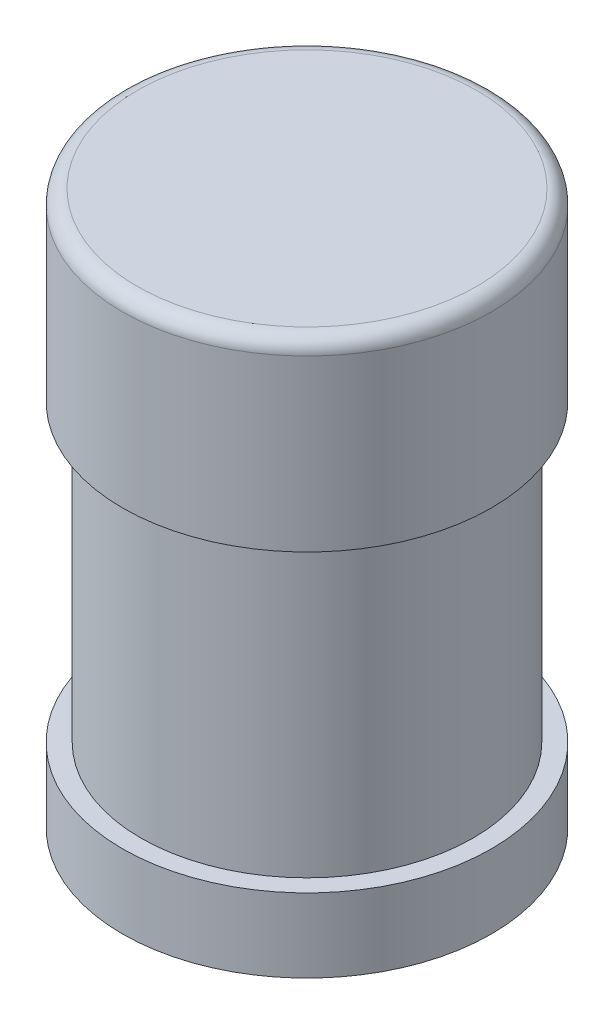
SolidWorks part; units mm, degrees
material "Plain Carbon Steel"
ref_plane "Front Plane" through (0, 0, 0) normal (0, 0, 1) x (1, 0, 0)
ref_plane "Top Plane" through (0, 0, 0) normal (0, 1, 0) x (1, 0, 0)
ref_plane "Right Plane" through (0, 0, 0) normal (1, 0, 0) x (0, 0, -1)
sketch "Sketch1" plane through (0, 0, 0) normal (0, 0, 1) x (1, 0, 0)
  line L0 (0, 0) -> (0, 15) construction
  line L1 (0, 15) -> (-5, 15)
  line L2 (-5, 15) -> (-5, 10)
  line L3 (-5, 10) -> (-4.5, 10)
  line L4 (-4.5, 10) -> (-4.5, 2)
  line L5 (-4.5, 2) -> (-5, 2)
  line L6 (-5, 2) -> (-5, 0)
  line L7 (-5, 0) -> (0, 0)
  line L8 (0, 0) -> (0, 15)
  dimension "D1" = 5
  dimension "D2" = 5
  dimension "D3" = 2
  dimension "D4" = 5
  dimension "D5" = 0.5
revolve "Revolve2" add sketch "Sketch1" angle 360 about L8
shell "Shell4" thickness 1
fillet "Fillet1" radius 0.4 1 edges at (0, 15, -5)
fillet "Fillet2" radius 0.4 1 edges at (0, 1, -3.5)
fillet "Fillet3" radius 0.4 1 edges at (0, 11, 3.5)
